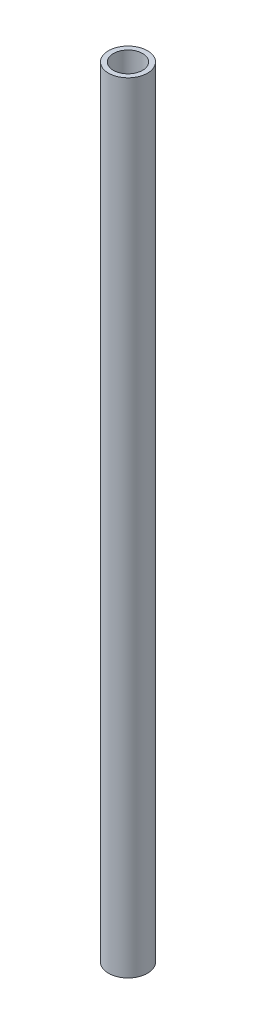
SolidWorks part; units mm, degrees
ref_plane "Front Plane" through (0, 0, 0) normal (0, 0, 1) x (1, 0, 0)
ref_plane "Top Plane" through (0, 0, 0) normal (0, 1, 0) x (1, 0, 0)
ref_plane "Right Plane" through (0, 0, 0) normal (1, 0, 0) x (0, 0, -1)
sketch "Sketch1" plane through (0, 0, 0) normal (0, 1, 0) x (1, 0, 0)
  circle A0 centre (0, 0) radius 4
  circle A1 centre (0, 0) radius 3
  dimension "D1" = 8
  dimension "D2" = 1
extrude "Boss-Extrude1" add sketch "Sketch1" along normal blind 160
